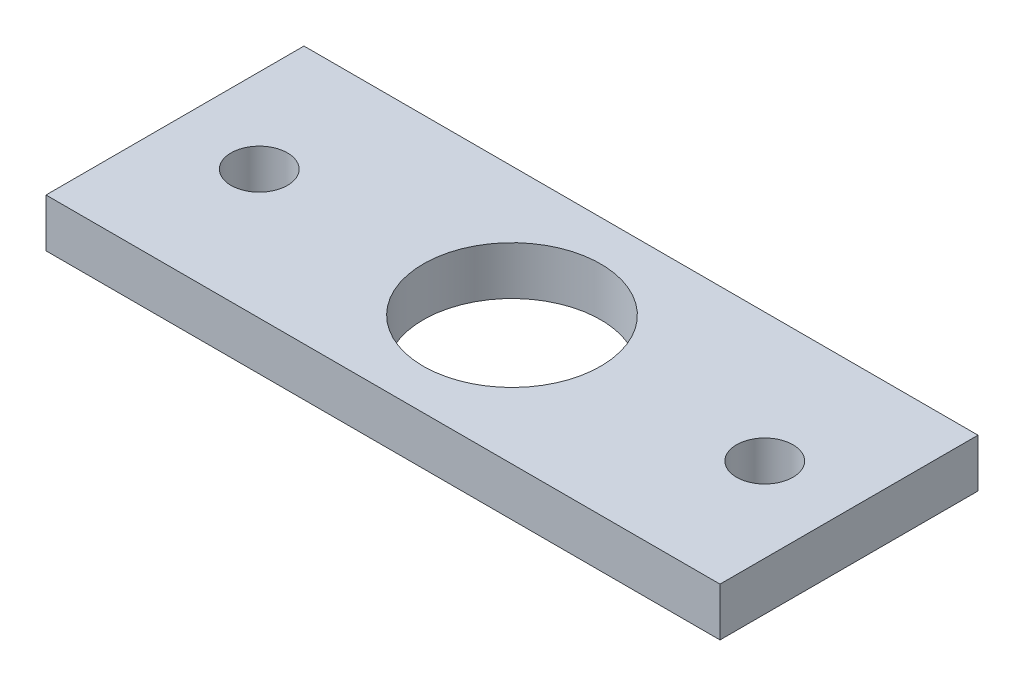
SolidWorks part; units mm, degrees
ref_plane "Front Plane" through (0, 0, 0) normal (0, 0, 1) x (1, 0, 0)
ref_plane "Top Plane" through (0, 0, 0) normal (0, 1, 0) x (1, 0, 0)
ref_plane "Right Plane" through (0, 0, 0) normal (1, 0, 0) x (0, 0, -1)
sketch "Sketch1" plane through (0, 0, 0) normal (0, 1, 0) x (1, 0, 0)
  line L0 (0, 14.9855) -> (0, -14.5762) construction
  line L1 (-20.9, -8) -> (20.9, -8)
  line L2 (-20.9, -8) -> (-20.9, 8)
  line L3 (-20.9, 8) -> (20.9, 8)
  line L4 (20.9, -8) -> (20.9, 8)
  line L5 (-20.4683, 0) -> (27.4527, 0) construction
  circle A0 centre (-15.675, 0) radius 1.75
  circle A1 centre (15.675, 0) radius 1.75
  circle A2 centre (0, 0) radius 9.5
  circle A3 centre (0, 0) radius 4.5
  circle A4 centre (0, 0) radius 5.5
  point P0 (0, 0)
  dimension "D3" = 19
  dimension "D4" = 3.5
  dimension "D6" = 9
  dimension "D7" = 11
  dimension "D1" = 41.8
  dimension "D2" = 16
  dimension "D5" = 15.675
extrude "Boss-Extrude1" add sketch "Sketch1" along normal blind 3 contours L1 A2 L3 | A2 L1 L4 L3 A1 | A2 L3 L2 L1 A0
equation "\"Bearing Outer Radius\"= 19"
equation "\"Plate Length\" = \"Bearing Outer Radius\" * 2.2"
equation "\"Plate Width\" = \"Bearing Outer Radius\" - 3"
equation "\"Bearing Inner Radius\"= 9"
equation "\"D2@Sketch1\"=\"Plate Width\""
equation "\"D3@Sketch1\"=\"Bearing Outer Radius\""
equation "\"D1@Sketch1\"=\"Plate Length\""
equation "\"D6@Sketch1\"=\"Bearing Inner Radius\""
equation "\"D7@Sketch1\"=\"Bearing Inner Radius\" + 2"
equation "\"D5@Sketch1\"=\"Plate Length\" * 3/8"
